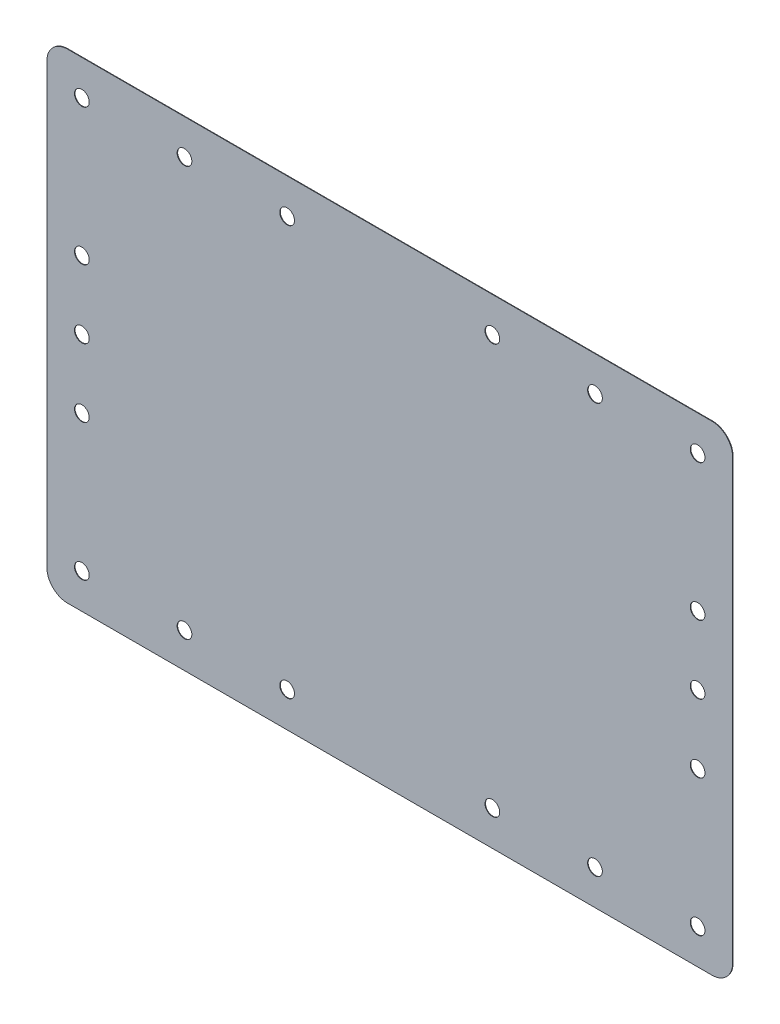
SolidWorks part; units mm, degrees
ref_plane "Front Plane" through (0, 0, 0) normal (0, 0, 1) x (1, 0, 0)
ref_plane "Top Plane" through (0, 0, 0) normal (0, 1, 0) x (1, 0, 0)
ref_plane "Right Plane" through (0, 0, 0) normal (1, 0, 0) x (0, 0, -1)
sketch "Model" plane through (0, 0, 0) normal (0, 0, 1) x (1, 0, 0)
  line L0 (-82.8082, 52.939) -> (-82.8082, -52.939)
  line L1 (82.8082, -52.939) -> (82.8082, 52.939)
  line L2 (-77.814, -57.9332) -> (77.814, -57.9332)
  line L3 (77.814, 57.9332) -> (-77.814, 57.9332)
  line L61 (77.814, 57.9321) -> (-77.814, 57.9321)
  line L62 (-77.814, -57.9321) -> (77.814, -57.9321)
  line L63 (-82.8071, 52.939) -> (-82.8071, -52.939)
  line L64 (82.8071, -52.939) -> (82.8071, 52.939)
  line L65 (-82.8082, -52.939) -> (-82.8071, -52.939)
  line L66 (-77.814, -57.9332) -> (-77.814, -57.9321)
  line L67 (-77.814, 57.9321) -> (-77.814, 57.9332)
  line L68 (-82.8082, 52.939) -> (-82.8071, 52.939)
  line L69 (77.814, -57.9332) -> (77.814, -57.9321)
  line L70 (82.8071, -52.939) -> (82.8082, -52.939)
  line L71 (77.814, 57.9321) -> (77.814, 57.9332)
  line L72 (82.8071, 52.939) -> (82.8082, 52.939)
  circle A0 centre (-74.348, 49.473) radius 1.775
  circle A1 centre (-24.7827, 49.473) radius 1.775
  circle A2 centre (24.7827, 49.473) radius 1.775
  circle A3 centre (74.348, 49.473) radius 1.775
  circle A4 centre (74.348, 16.491) radius 1.775
  circle A5 centre (74.348, -16.491) radius 1.775
  circle A6 centre (74.348, -49.473) radius 1.775
  circle A7 centre (24.7827, -49.473) radius 1.775
  circle A8 centre (-24.7827, -49.473) radius 1.775
  circle A9 centre (-74.348, -49.473) radius 1.775
  circle A10 centre (-74.348, -16.491) radius 1.775
  circle A11 centre (-74.348, 16.491) radius 1.775
  circle A12 centre (49.5654, -49.473) radius 1.775
  circle A13 centre (-49.5654, -49.473) radius 1.775
  circle A14 centre (-49.5654, 49.473) radius 1.775
  circle A15 centre (49.5654, 49.473) radius 1.775
  circle A16 centre (-74.348, 0) radius 1.775
  circle A17 centre (74.348, 0) radius 1.775
  arc A42 (-77.814, 57.9321) -> (-82.8071, 52.939) centre (-77.8133, 52.9383) ccw
  arc A43 (-82.8071, -52.939) -> (-77.814, -57.9321) centre (-77.8133, -52.9383) ccw
  arc A44 (77.814, -57.9321) -> (82.8071, -52.939) centre (77.8133, -52.9383) ccw
  arc A45 (82.8071, 52.939) -> (77.814, 57.9321) centre (77.8133, 52.9383) ccw
extrude "Boss-Extrude1" add sketch "Model" along normal blind 0.127 contours L64 A45 L61 A42 L63 A43 L62 A44 A0 A1 A2 A3 A4 A5 A6 A7 A8 A9 A10 A11 A12 A13 A14 A15 A16 A17
